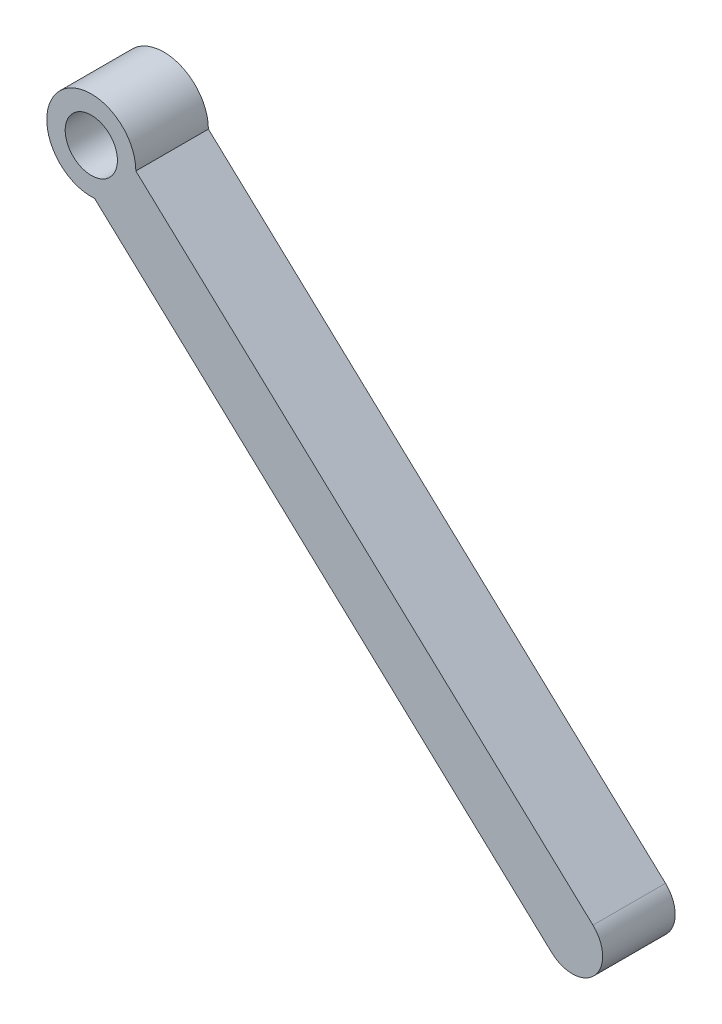
SolidWorks part; units mm, degrees
ref_plane "Face" through (0, 0, 0) normal (0, 0, 1) x (1, 0, 0)
ref_plane "Dessus" through (0, 0, 0) normal (0, 1, 0) x (1, 0, 0)
ref_plane "Droite" through (0, 0, 0) normal (1, 0, 0) x (0, 0, -1)
sketch "Esquisse2" plane through (0, 0, 0) normal (0, 0, 1) x (1, 0, 0)
  line L2 (-13.9157, 15.6717) -> (17.591, -13.5914)
  line L3 (-20.0542, 15.6717) -> (14.7481, -16.6522)
  circle A7 centre (-16.985, 15.6717) radius 3.0692
  arc A8 (17.591, -13.5914) -> (14.7481, -16.6522) centre (16.1696, -15.1218) cw
  arc A9 (-13.9157, 15.6717) -> (-20.0542, 15.6717) centre (-16.985, 15.6717) ccw
  circle A10 centre (-16.985, 15.6717) radius 1.8
  dimension "D2" = 3.6
  dimension "D1" = 43
extrude "Boss.-Extru.2" add sketch "Esquisse2" along normal blind 5 contours A8 L2 A7 L3 | L3 A7 | A7 L3 A10
